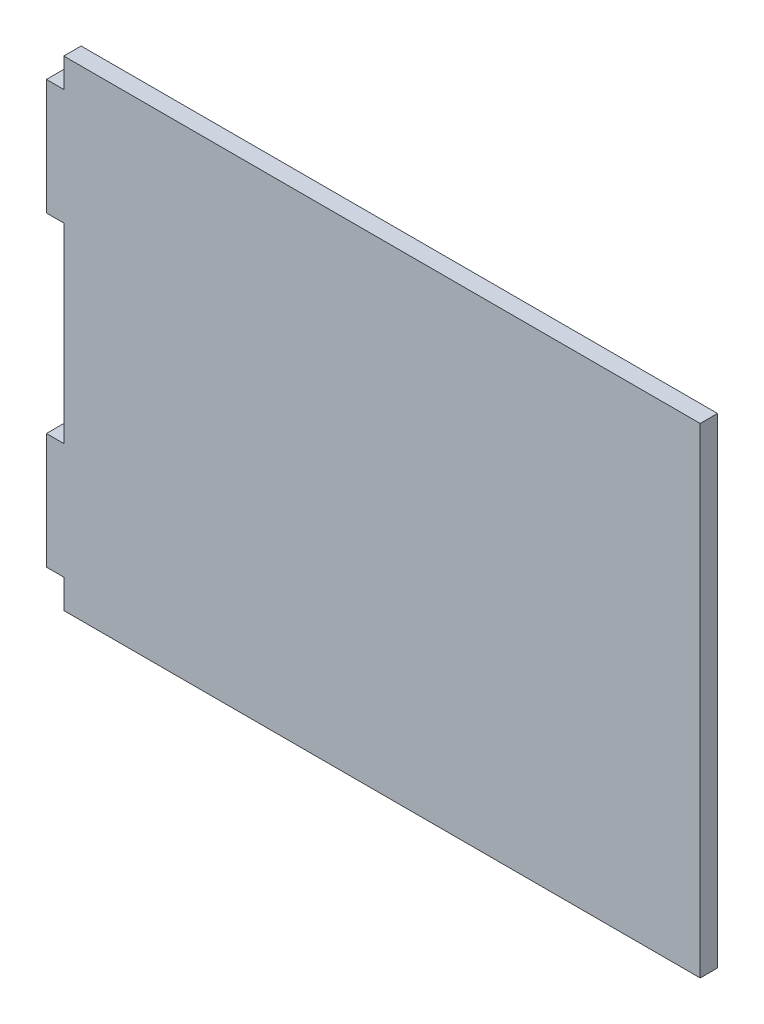
SolidWorks part; units mm, degrees
material "Carvalho"
ref_plane "Plano frontal" through (0, 0, 0) normal (0, 0, 1) x (1, 0, 0)
ref_plane "Plano superior" through (0, 0, 0) normal (0, 1, 0) x (1, 0, 0)
ref_plane "Plano direito" through (0, 0, 0) normal (1, 0, 0) x (0, 0, -1)
sketch "Esboço1" plane through (0, 0, 0) normal (0, 0, 1) x (1, 0, 0)
  line L0 (-55.3612, 7.2393) -> (-55.3612, -25.7607)
  line L1 (-55.3612, 32.2393) -> (54.6388, 32.2393)
  line L2 (-55.3612, 32.2393) -> (-55.3612, 27.2393)
  line L3 (-55.3612, -50.7607) -> (54.6388, -50.7607)
  line L4 (54.6388, 32.2393) -> (54.6388, -50.7607)
  line L5 (-55.3612, -45.7607) -> (-58.3612, -45.7607)
  line L7 (-55.3612, -25.7607) -> (-58.3612, -25.7607)
  line L8 (-58.3612, -45.7607) -> (-58.3612, -25.7607)
  line L9 (-55.3612, 7.2393) -> (-58.3612, 7.2393)
  line L10 (-55.3612, -45.7607) -> (-55.3612, -50.7607)
  line L11 (-55.3612, 27.2393) -> (-58.3612, 27.2393)
  line L12 (-58.3612, 7.2393) -> (-58.3612, 27.2393)
  dimension "D1" = 83
  dimension "D2" = 3
  dimension "D3" = 3
  dimension "D4" = 20
  dimension "D5" = 5
  dimension "D6" = 5
  dimension "D7" = 20
  dimension "D8" = 110
extrude "Ressalto-extrusão1" add sketch "Esboço1" along normal blind 3
equation "\"w\"=10"
